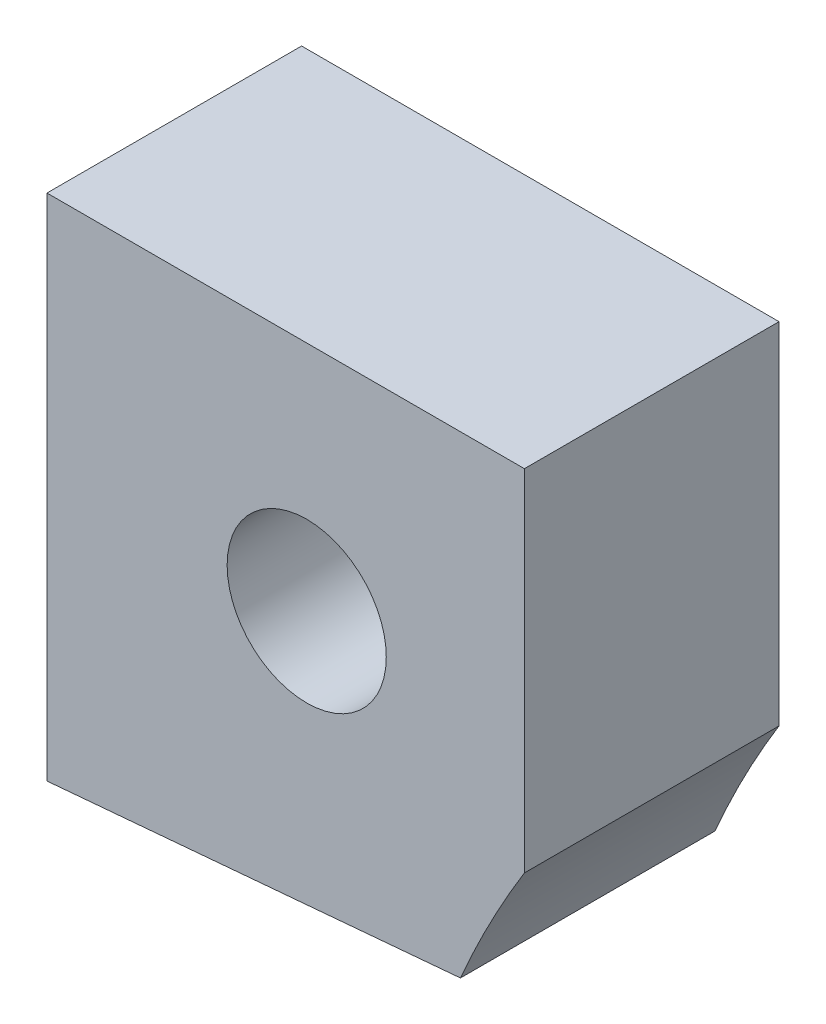
SolidWorks part; units mm, degrees
ref_plane "前视基准面" through (0, 0, 0) normal (0, 0, 1) x (1, 0, 0)
ref_plane "上视基准面" through (0, 0, 0) normal (0, 1, 0) x (1, 0, 0)
ref_plane "右视基准面" through (0, 0, 0) normal (1, 0, 0) x (0, 0, -1)
sketch "草图1" plane through (0, 0, 0) normal (0, 0, 1) x (1, 0, 0)
  line L0 (-51.3264, 0) -> (-1.8413, 0) construction
  line L1 (26.3068, 11) -> (26.3068, 0)
  line L2 (26.3068, 11) -> (11.3068, 11)
  line L3 (11.3068, 11) -> (11.3068, -5)
  line L4 (12.7145, 14.3572) -> (-9.9978, -13.8163) construction
  line L5 (11.3068, -5) -> (24.2968, -3.8635)
  line L6 (26.3068, 11) -> (11.3068, -5) construction
  line L8 (16.5615, 0) -> (50.8898, 0) construction
  arc A0 (24.2968, -3.8635) -> (26.3068, 0) centre (51.8453, -15.7411) cw
  circle A1 centre (19.4674, 3.7046) radius 1.5
  dimension "D5" = 30
  dimension "D7" = 3
  dimension "D1" = 11
  dimension "D2" = 15
  dimension "D3" = 16
  dimension "D4" = 12.99
  dimension "D6" = 85
  dimension "D8" = 10
extrude "凸台-拉伸1" add sketch "草图1" along normal blind 8
cosmetic thread "装饰螺纹线1" parameters "D2"=9
sketch "草图2" plane through (0, 0, 8) normal (0, 0, 1) x (1, 0, 0)
  line L0 (26.3068, 11) -> (11.3068, -5) construction
  circle A0 centre (19.4674, 3.7046) radius 2.5
  dimension "D1" = 5
  dimension "D2" = 10
extrude "切除-拉伸1" cut sketch "草图2" against normal blind 4
